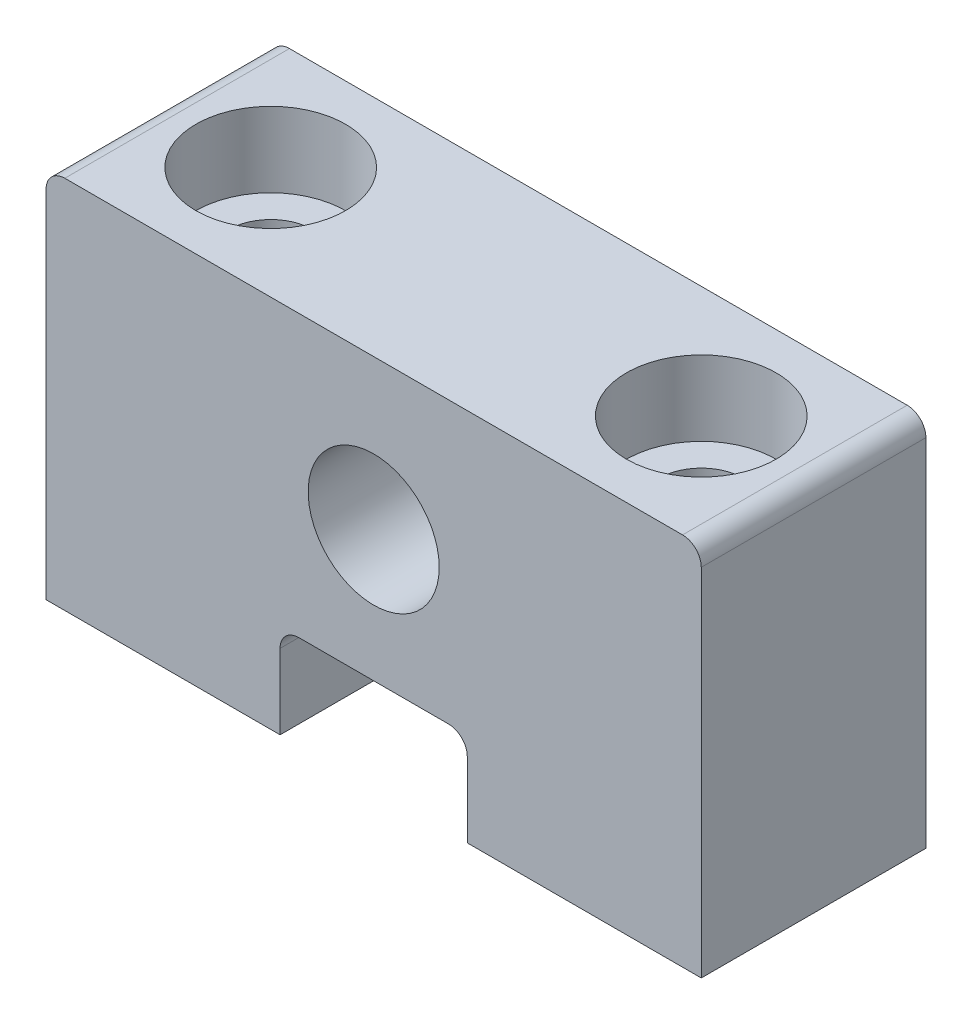
SolidWorks part; units mm, degrees
ref_plane "Front Plane" through (0, 0, 0) normal (0, 0, 1) x (1, 0, 0)
ref_plane "Top Plane" through (0, 0, 0) normal (0, 1, 0) x (1, 0, 0)
ref_plane "Right Plane" through (0, 0, 0) normal (1, 0, 0) x (0, 0, -1)
sketch "Sketch1" plane through (0, 0, 0) normal (0, 0, 1) x (1, 0, 0)
  line L0 (0, -26.1041) -> (0, 52.7781) construction
  line L1 (-17.5, 20) -> (17.5, 20)
  line L3 (-5, 0) -> (-17.5, 0)
  line L4 (17.5, 0) -> (17.5, 20)
  line L6 (-5, 0) -> (-5, 5)
  line L7 (-17.5, 0) -> (-17.5, 20)
  line L8 (5, 0) -> (17.5, 0)
  line L9 (-5, 5) -> (5, 5)
  line L10 (5, 0) -> (5, 5)
  circle A0 centre (0, 12) radius 3.5
  point P4 (0, 0)
  point P5 (0, 0)
  point P6 (0, 0)
  point P7 (-12.5, 25)
  point P9 (12.5, 25)
  point P15 (0, 8.5)
  point P23 (5, 2.5)
  dimension "D6" = 7
  dimension "D3" = 5
  dimension "D2" = 8
  dimension "D1" = 20
  dimension "D4" = 10
  dimension "D7" = 35
extrude "Boss-Extrude1" add sketch "Sketch1" along normal blind 12
sketch "Sketch2" plane through (0, 20, 0) normal (0, 1, 0) x (1, 0, 0)
  line L0 (5, -12) -> (5, 0) construction
  line L1 (-5, -12) -> (-5, 0) construction
  line L2 (5, -12) -> (5, 0)
  line L3 (-5, -12) -> (-5, 0)
  line L4 (0, 0) -> (0, -12) construction
  line L5 (17.5, 0) -> (-17.5, 0) construction
  line L6 (17.5, -12) -> (-17.5, -12) construction
  line L7 (-17.5, -6) -> (17.5, -6) construction
  line L8 (-17.5, -12) -> (-17.5, 0) construction
  line L9 (17.5, -12) -> (17.5, 0) construction
  point P0 (-11.5, -6)
  point P1 (11.5, -6)
  point P12 (0, 0)
  dimension "D1" = 6.5
hole_wizard "CBORE for M4 SHCS1" positions "Sketch3" profile "Sketch4" counterbore size "M4" standard "ANSI Metric" end condition through all
sketch "Sketch3" plane through (0, 20, 0) normal (0, 1, 0) x (1, 0, 0)
  point P0 (-11.5, -6)
  point P3 (11.5, -6)
sketch "Sketch4" plane through (-11.5, 20, 6) normal (1, 0, 0) x (0, 0, 1)
  line L0 (0, 0) -> (0, 20)
  line L1 (0, 20) -> (2.25, 20)
  line L3 (2.25, 20) -> (2.25, 4)
  line L4 (2.25, 4) -> (4, 4)
  line L5 (4, 4) -> (4, 0)
  line L7 (4, 0) -> (0, 0)
  line L11 (0, -6.35) -> (0, 107.95) construction
  dimension "Thru Hole Dia." = 4.5
  dimension "Thru Hole Depth" = 20
  dimension "C'Bore Dia." = 8
  dimension "C'Bore Depth" = 4
fillet "Fillet1" radius 1 4 edges at (5, 5, 6) (-5, 5, 6) (17.5, 20, 6) (-17.5, 20, 6)
equation "\"0.095inin\"=0.085"
